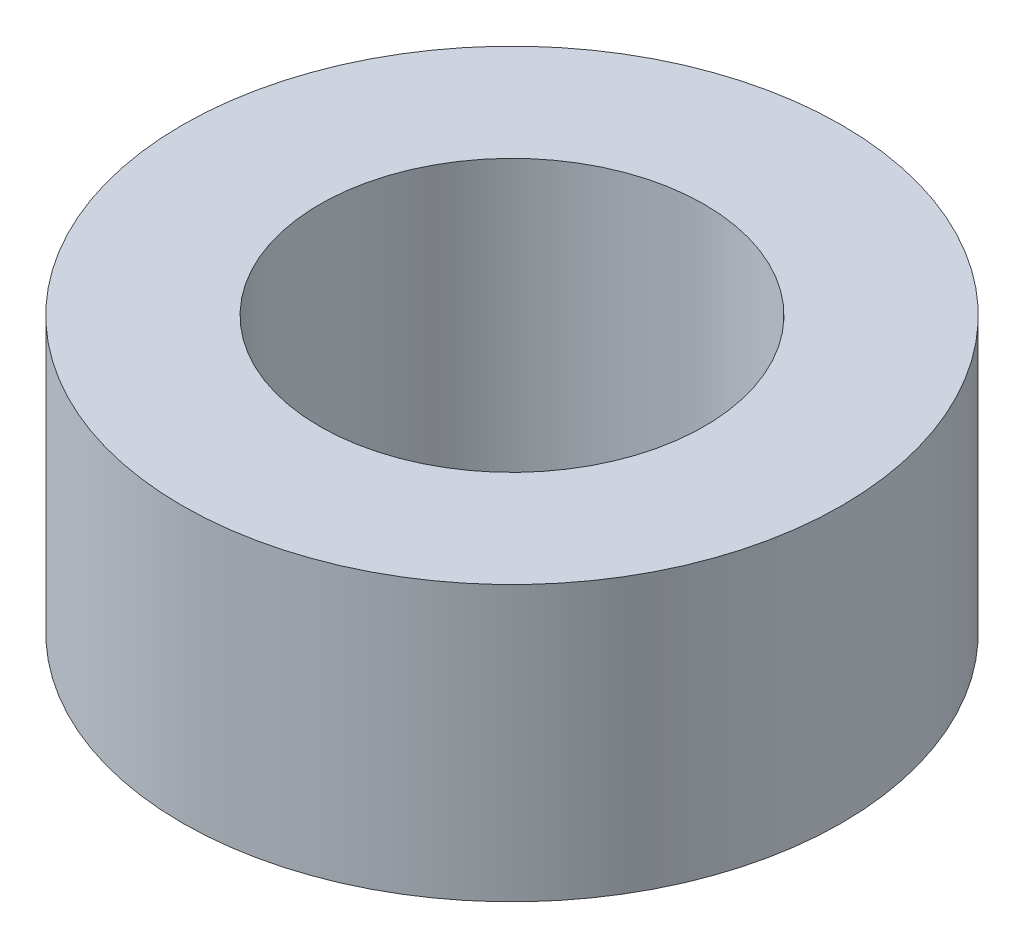
SolidWorks part; units mm, degrees
ref_plane "Front Plane" through (0, 0, 0) normal (0, 0, 1) x (1, 0, 0)
ref_plane "Top Plane" through (0, 0, 0) normal (0, 1, 0) x (1, 0, 0)
ref_plane "Right Plane" through (0, 0, 0) normal (1, 0, 0) x (0, 0, -1)
sketch "Sketch1" plane through (0, 0, 0) normal (0, 1, 0) x (1, 0, 0)
  circle A0 centre (0, 0) radius 7
  circle A1 centre (0, 0) radius 12
  dimension "D1" = 14
  dimension "D2" = 5
extrude "Boss-Extrude1" add sketch "Sketch1" along normal blind 10
